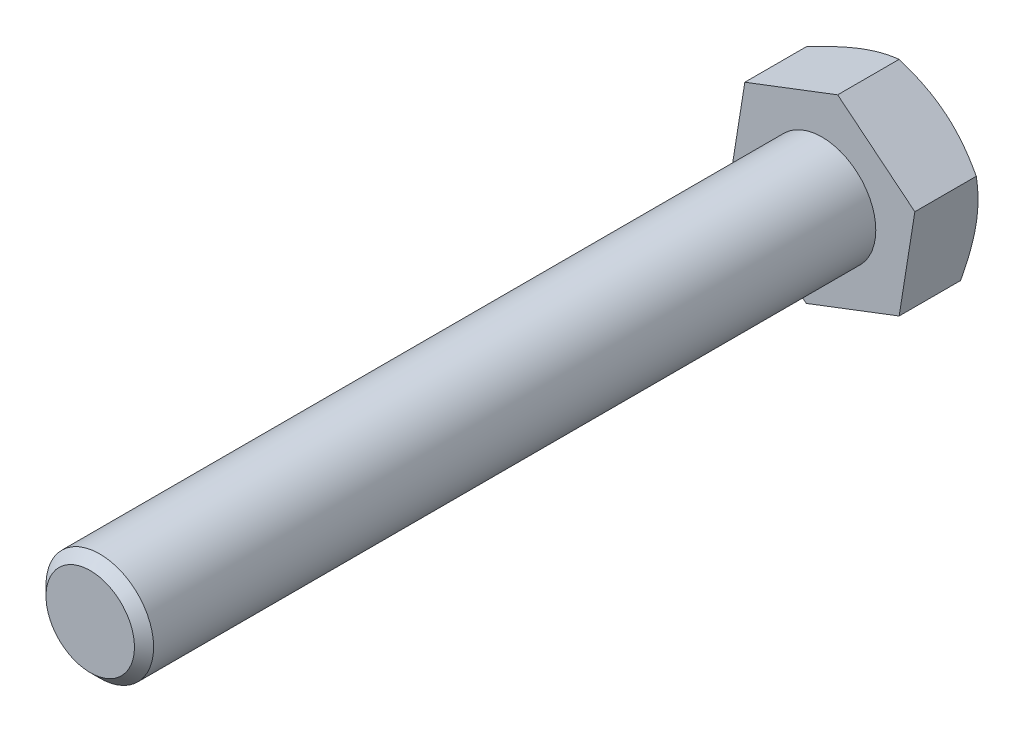
SolidWorks part; units mm, degrees
material "Сталь"
ref_plane "Спереди" through (0, 0, 0) normal (0, 0, 1) x (1, 0, 0)
ref_plane "Сверху" through (0, 0, 0) normal (0, 1, 0) x (1, 0, 0)
ref_plane "Справа" through (0, 0, 0) normal (1, 0, 0) x (0, 0, -1)
sketch "Эскиз1" plane through (0, 0, 0) normal (0, 0, 1) x (1, 0, 0)
  line L1 (0.7283, 4.561) -> (-3.5858, 2.9112)
  line L2 (-3.5858, 2.9112) -> (-4.3141, -1.6498)
  line L3 (-4.3141, -1.6498) -> (-0.7283, -4.561)
  line L4 (-0.7283, -4.561) -> (3.5858, -2.9112)
  line L5 (3.5858, -2.9112) -> (4.3141, 1.6498)
  line L6 (4.3141, 1.6498) -> (0.7283, 4.561)
  circle A0 centre (0, 0) radius 4 construction
  dimension "D1" = 8
extrude "Бобышка-Вытянуть1" add sketch "Эскиз1" along normal blind 3.5
sketch "Эскиз2" plane through (0, 0, 3.5) normal (0, 0, 1) x (1, 0, 0)
  circle A0 centre (0, 0) radius 2.5
  dimension "D1" = 5
extrude "Бобышка-Вытянуть2" add sketch "Эскиз2" along normal blind 34
cosmetic thread "Условное изображение резьбы1" parameters "D1"=12, "D2"=4.11
chamfer "Фаска1" distance 0.445 angle 45 1 edges at (2.5, 0, 37.5)
sketch "Эскиз4" plane through (0, 0, 0) normal (0, 1, 0) x (1, 0, 0)
  line L0 (3.5, 0) -> (7.5, 0)
  line L1 (7.5, 0) -> (7.5, -2.3094)
  line L2 (7.5, -2.3094) -> (3.5, 0)
  line L3 (4.3141, 0) -> (0.7283, 0) construction
  line L4 (0, 0) -> (0, -3.5) construction
  line L5 (0.7283, -3.5) -> (-3.5858, -3.5) construction
  dimension "D1" = 3.5
  dimension "D2" = 4
  dimension "D3" = 30
revolve "Вырез-Повернуть1" cut sketch "Эскиз4" angle 360 about L4
